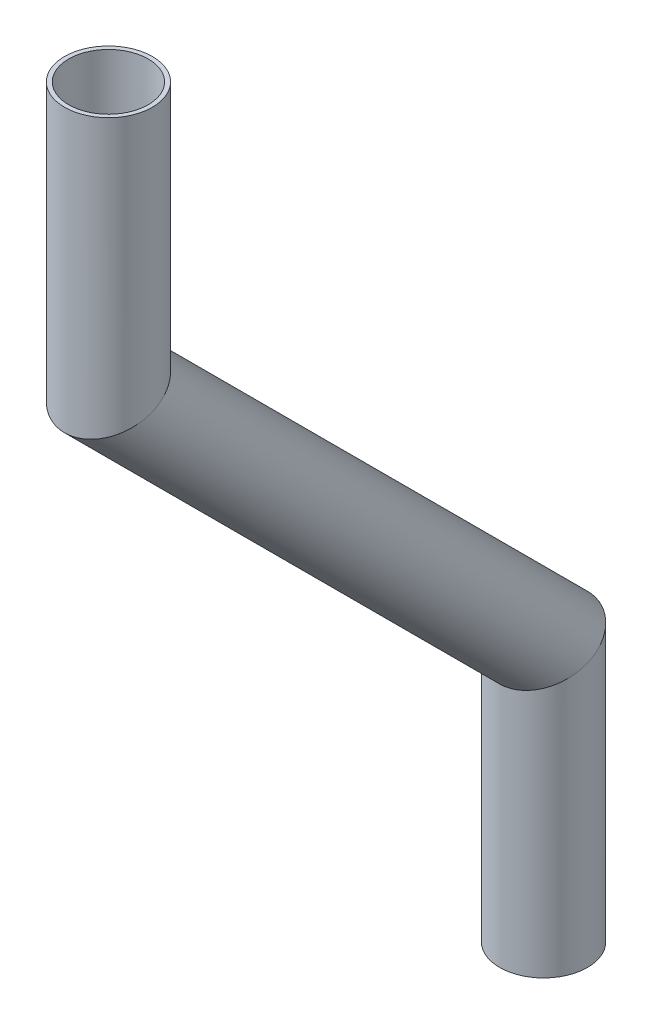
SolidWorks part; units mm, degrees
ref_plane "Front Plane" through (0, 0, 0) normal (0, 0, 1) x (1, 0, 0)
ref_plane "Top Plane" through (0, 0, 0) normal (0, 1, 0) x (1, 0, 0)
ref_plane "Right Plane" through (0, 0, 0) normal (1, 0, 0) x (0, 0, -1)
sketch "Sketch1" plane through (0, 0, 0) normal (1, 0, 0) x (0, 0, -1)
  line L0 (-307.5983, -50.5162) -> (-307.5983, -88.6162)
  line L1 (-307.5983, -88.6162) -> (-244.7365, -151.478)
  line L2 (-244.7365, -151.478) -> (-244.7365, -189.578)
  line L3 (-307.5983, -88.6162) -> (-307.5983, -130.7988) construction
  dimension "D1" = 45
  dimension "D2" = 38.1
  dimension "D3" = 38.1
  dimension "D4" = 88.9
other "Pipe 0.5 SCH 40(1)"
ref_plane "Plane1" through (0, -50.5162, 307.5983) normal (0, -1, 0) x (0, 0, -1)
sketch "Sketch11" plane through (0, -50.5162, 307.5983) normal (0, -1, 0) x (0, 0, -1)
  circle A0 centre (0, 0) radius 5.7404
  circle A1 centre (0, 0) radius 6.35
  point P5 (0, 0)
  dimension "In_dia" = 11.4808
  dimension "Out_dia" = 12.7
